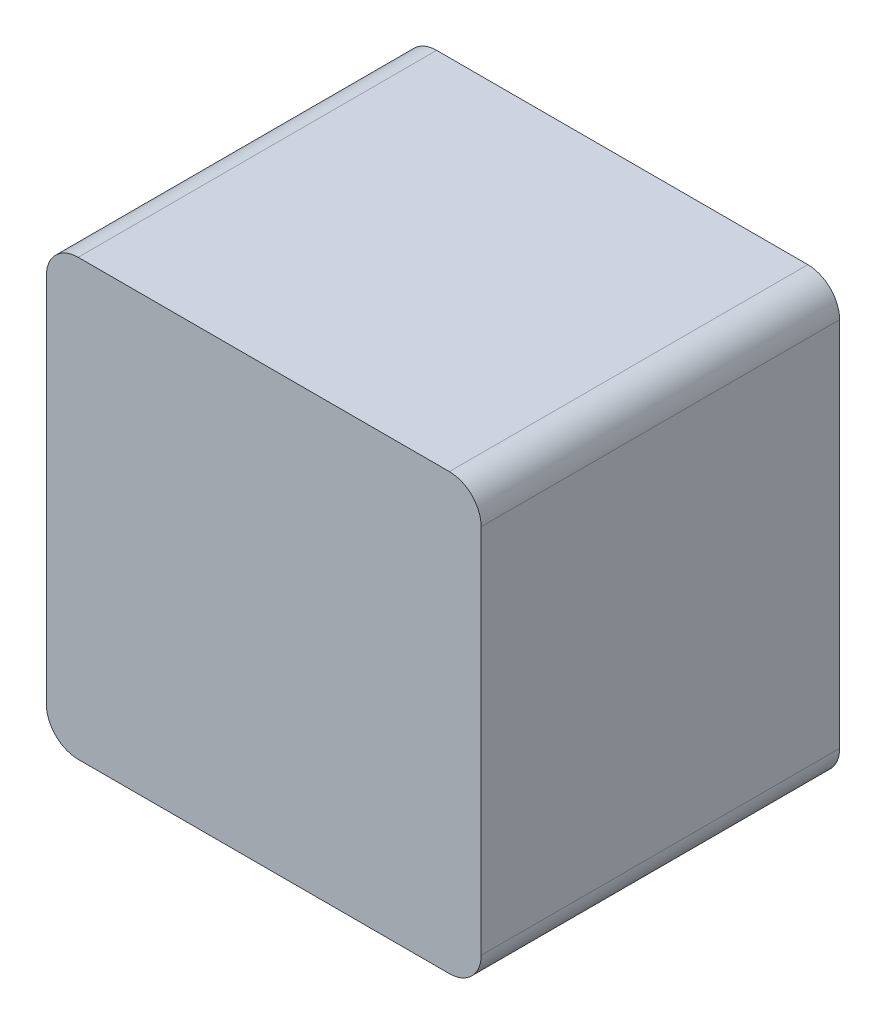
SolidWorks part; units mm, degrees
ref_plane "Front Plane" through (0, 0, 0) normal (0, 0, 1) x (1, 0, 0)
ref_plane "Top Plane" through (0, 0, 0) normal (0, 1, 0) x (1, 0, 0)
ref_plane "Right Plane" through (0, 0, 0) normal (1, 0, 0) x (0, 0, -1)
sketch "Sketch1" plane through (0, 0, 0) normal (0, 0, 1) x (1, 0, 0)
  line L0 (75, -223) -> (75, -182) construction
  line L1 (34, -223) -> (75, -223) construction
  line L2 (34, -182) -> (34, -223) construction
  line L3 (75, -182) -> (34, -182) construction
  line L4 (75, -223) -> (75, -182)
  line L5 (34, -223) -> (75, -223)
  line L6 (34, -182) -> (34, -223)
  line L7 (75, -182) -> (34, -182)
extrude "Boss-Extrude1" add sketch "Sketch1" along normal blind 33.8
sketch "Sketch2" plane through (0, 0, 0) normal (0, 0, -1) x (-1, 0, 0)
  circle A0 centre (-54.5, -202.5) radius 5 construction
  circle A1 centre (-54.5, -202.5) radius 5
  circle A2 centre (-54.5, -202.5) radius 4.9
  dimension "D1" = 0.1
extrude "Boss-Extrude2" add sketch "Sketch2" along normal blind 15 separate body
fillet "Fillet1" radius 3 4 edges at (75, -182, 16.9) (75, -223, 16.9) (34, -223, 16.9) (34, -182, 16.9)
